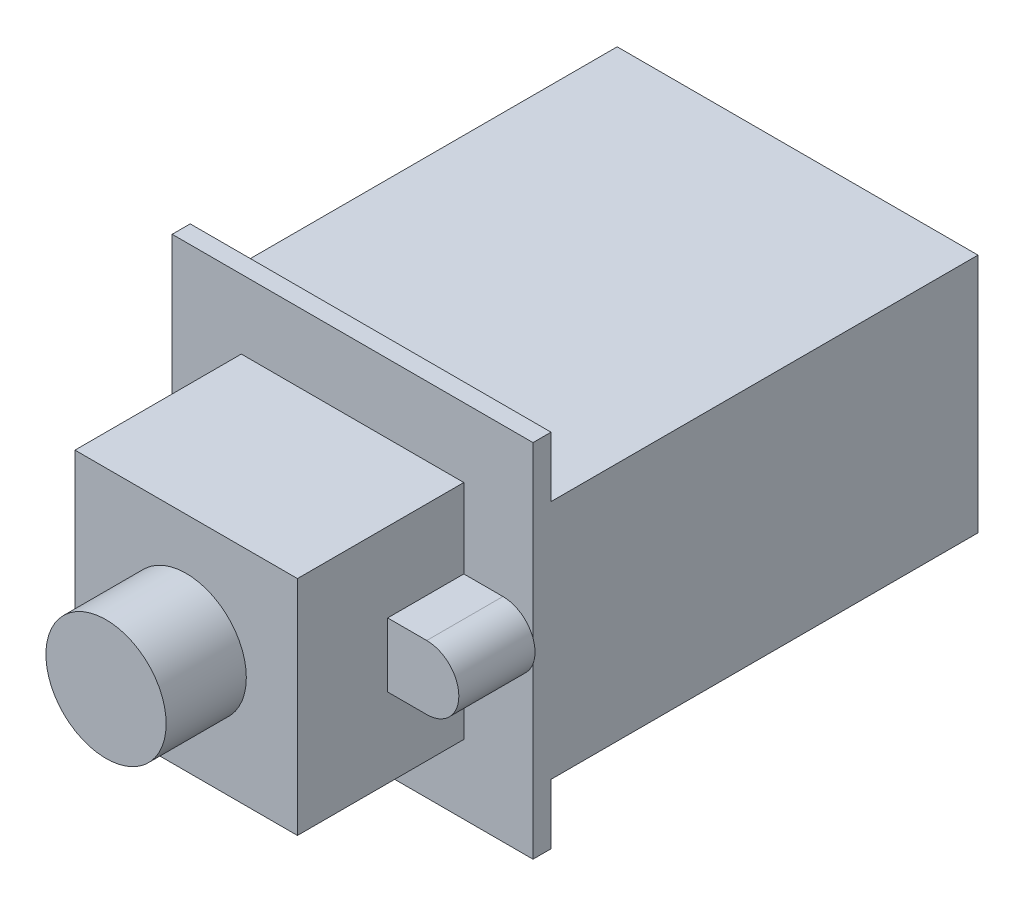
SolidWorks part; units mm, degrees
ref_plane "Front Plane" through (0, 0, 0) normal (0, 0, 1) x (1, 0, 0)
ref_plane "Top Plane" through (0, 0, 0) normal (0, 1, 0) x (1, 0, 0)
ref_plane "Right Plane" through (0, 0, 0) normal (1, 0, 0) x (0, 0, -1)
sketch "Sketch1" plane through (0, 0, 0) normal (0, 0, 1) x (1, 0, 0)
  line L1 (-7.0485, -7.0485) -> (7.0485, -7.0485)
  line L2 (-7.0485, -7.0485) -> (-7.0485, 7.0485)
  line L3 (-7.0485, 7.0485) -> (7.0485, 7.0485)
  line L4 (7.0485, -7.0485) -> (7.0485, 7.0485)
  line L5 (0, 7.0485) -> (0, -7.0485) construction
  line L6 (-7.0485, 0) -> (7.0485, 0) construction
  point P0 (0, 0)
  dimension "D1" = 14.097
extrude "Boss-Extrude1" add sketch "Sketch1" along normal blind 10.541
sketch "Sketch2" plane through (0, 0, 10.541) normal (0, 0, 1) x (1, 0, 0)
  circle A0 centre (0, 0) radius 3.81
  dimension "D1" = 7.62
extrude "Boss-Extrude2" add sketch "Sketch2" along normal blind 5.08
sketch "Sketch3" plane through (0, 0, 0) normal (0, 0, -1) x (-1, 0, 0)
  line L0 (-9.525, 2.032) -> (-7.0485, 2.032)
  line L1 (-7.0485, -7.0485) -> (-7.0485, 7.0485) construction
  line L2 (-7.0485, 2.032) -> (-7.0485, -2.032)
  line L3 (-7.0485, -2.032) -> (-9.525, -2.032)
  arc A0 (-9.525, 2.032) -> (-9.525, -2.032) centre (-9.525, 0) ccw
  dimension "D1" = 11.557
  dimension "D2" = 4.064
extrude "Boss-Extrude3" add sketch "Sketch3" against normal blind 4.826
mirror "Mirror1" about plane through (0, 0, 0) normal (1, 0, 0) of "Boss-Extrude3"
sketch "Sketch4" plane through (0, 0, 0) normal (0, 0, -1) x (-1, 0, 0)
  line L1 (-11.43, -11.43) -> (11.43, -11.43)
  line L2 (-11.43, -11.43) -> (-11.43, 11.43)
  line L3 (-11.43, 11.43) -> (11.43, 11.43)
  line L4 (11.43, -11.43) -> (11.43, 11.43)
  line L5 (0, 11.43) -> (0, -11.43) construction
  line L6 (-11.43, 0) -> (11.43, 0) construction
  point P0 (0, 0)
  dimension "D1" = 22.86
extrude "Boss-Extrude4" add sketch "Sketch4" along normal blind 1.143
sketch "Sketch5" plane through (0, 0, -1.143) normal (0, 0, -1) x (-1, 0, 0)
  line L0 (11.43, -11.43) -> (11.43, 11.43) construction
  line L1 (-11.43, -7.62) -> (11.43, -7.62)
  line L2 (-11.43, -7.62) -> (-11.43, 7.62)
  line L3 (-11.43, 7.62) -> (11.43, 7.62)
  line L4 (11.43, -7.62) -> (11.43, 7.62)
  line L5 (0, 7.62) -> (0, -7.62) construction
  line L6 (-11.43, 0) -> (11.43, 0) construction
  point P0 (0, 0)
  dimension "D1" = 15.24
extrude "Boss-Extrude5" add sketch "Sketch5" along normal blind 27.051
